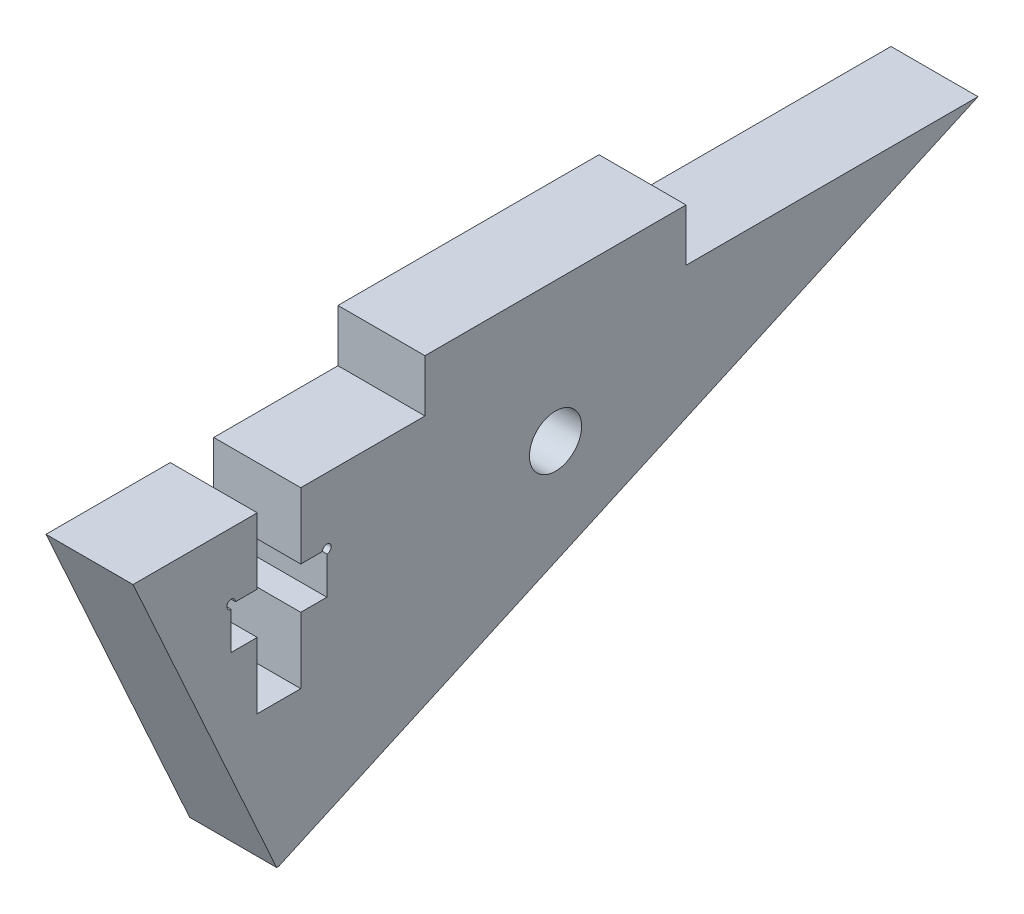
SolidWorks part; units mm, degrees
material "PMMA"
ref_plane "Front Plane" through (0, 0, 0) normal (0, 0, 1) x (1, 0, 0)
ref_plane "Top Plane" through (0, 0, 0) normal (0, 1, 0) x (1, 0, 0)
ref_plane "Right Plane" through (0, 0, 0) normal (1, 0, 0) x (0, 0, -1)
sketch "Schizzo1" plane through (0, 0, 0) normal (1, 0, 0) x (0, 0, -1)
  line L0 (-24.275, -9.105) -> (24.275, 9.105) construction
  line L1 (-24.275, 9.105) -> (24.275, 9.105)
  line L2 (-24.275, 9.105) -> (-24.275, -9.105)
  line L3 (-24.275, -9.105) -> (24.275, -9.105)
  line L4 (24.275, 9.105) -> (24.275, -9.105)
  point P4 (0, 0)
  dimension "D1" = 18.21
  dimension "D2" = 48.55
extrude "Estrusione-Estrusione1" add sketch "Schizzo1" along normal blind 5
sketch "Schizzo3" plane through (0, 0, 0) normal (1, 0, 0) x (0, 0, -1)
  line L1 (24.275, 9.105) -> (-24.275, 9.105) construction
  line L3 (0, 9.105) -> (0, -9.105) construction
  line L4 (-24.275, -9.105) -> (24.275, -9.105) construction
  circle A1 centre (0, 4.105) radius 1.5
  dimension "D5" = 5
sketch "Schizzo2" plane through (0, 0, 0) normal (1, 0, 0) x (0, 0, -1)
  line L0 (24.275, 9.105) -> (-15.906, -9.105)
  line L1 (-24.275, -9.105) -> (24.275, -9.105) construction
  line L2 (-15.906, -9.105) -> (24.275, -9.105)
  line L3 (24.275, -9.105) -> (24.275, 9.105)
  line L4 (-24.275, 9.105) -> (-24.275, -9.105)
  line L5 (-24.275, -9.105) -> (-16.0193, -9.1116)
  line L6 (-16.0193, -9.1116) -> (-24.275, 9.105)
  line L7 (24.275, 9.105) -> (-24.275, 9.105) construction
  dimension "D1" = 24.38
  dimension "D2" = 65.62
  dimension "D3" = 20
extrude "Taglio-Estrusione1" cut sketch "Schizzo2" along direction (1, 0, 0) on the side of the normal through all
extrude "Taglio-Estrusione2" cut sketch "Schizzo3" along direction (1, 0, 0) on the side of the normal through all
sketch "Schizzo4" plane through (0, 9.105, 0) normal (0, 1, 0) x (1, 0, 0)
  line L1 (5, 24.275) -> (5, -24.275) construction
  line L2 (0, 24.275) -> (0, -24.275) construction
  line L4 (5, 24.275) -> (0, 24.275) construction
  line L6 (5, 0) -> (0, 0) construction
  line L7 (0, 7.5) -> (5, 7.5)
  line L8 (0, 7.5) -> (0, -7.5)
  line L9 (0, -7.5) -> (5, -7.5)
  line L10 (5, 7.5) -> (5, -7.5)
  point P16 (5, 0)
  dimension "D2" = 16.775
  dimension "D3" = 15
extrude "Estrusione-Estrusione2" add sketch "Schizzo4" along normal blind 3
sketch "Schizzo6" plane through (0, 0, 0) normal (1, 0, 0) x (0, 0, -1)
  line L0 (-15.8875, -0.895) -> (-15.8875, 9.105) construction
  line L1 (-17.1375, -0.895) -> (-17.1375, 2.905)
  line L2 (-17.1375, 2.905) -> (-18.6375, 2.905)
  line L3 (-18.6375, 2.905) -> (-18.6375, 5.305)
  line L4 (-18.6375, 5.305) -> (-17.1375, 5.305)
  line L5 (-17.1375, 5.305) -> (-17.1375, 9.105)
  line L6 (-17.1375, 9.105) -> (-14.6375, 9.105)
  line L7 (-14.6375, 9.105) -> (-14.6375, 5.305)
  line L8 (-14.6375, 5.305) -> (-13.1375, 5.305)
  line L9 (-13.1375, 5.305) -> (-13.1375, 2.905)
  line L10 (-13.1375, 2.905) -> (-14.6375, 2.905)
  line L11 (-14.6375, 2.905) -> (-14.6375, -0.895)
  line L12 (-14.6375, -0.895) -> (-17.1375, -0.895)
  line L15 (-7.5, 9.105) -> (-24.275, 9.105) construction
  line L16 (-15.8875, 9.105) -> (-15.8875, -9.105) construction
  line L17 (-16.0222, -9.105) -> (-15.906, -9.105) construction
  point P14 (-15.8875, -0.895)
  dimension "D1" = 2.4
  dimension "D2" = 10
  dimension "D3" = 90
  dimension "D4" = 90
  dimension "D5" = 2.5
  dimension "D6" = 5.5
extrude "Taglio-Estrusione3" cut sketch "Schizzo6" along normal through all
sketch "Schizzo7" plane through (5, 0, 0) normal (1, 0, 0) x (0, 0, -1)
  circle A0 centre (-18.6375, 5.305) radius 0.25
  circle A1 centre (-13.1375, 5.305) radius 0.25
  dimension "D1" = 0.5
extrude "Taglio-Estrusione4" cut sketch "Schizzo7" against normal through all
equation "\"Thickness5\"= 5"
equation "\"D1@Estrusione-Estrusione1\"=\"Thickness5\""
equation "\"D1@Estrusione-Estrusione2\"=\"Thickness3\""
equation "\"Thickness3\"= 3"
